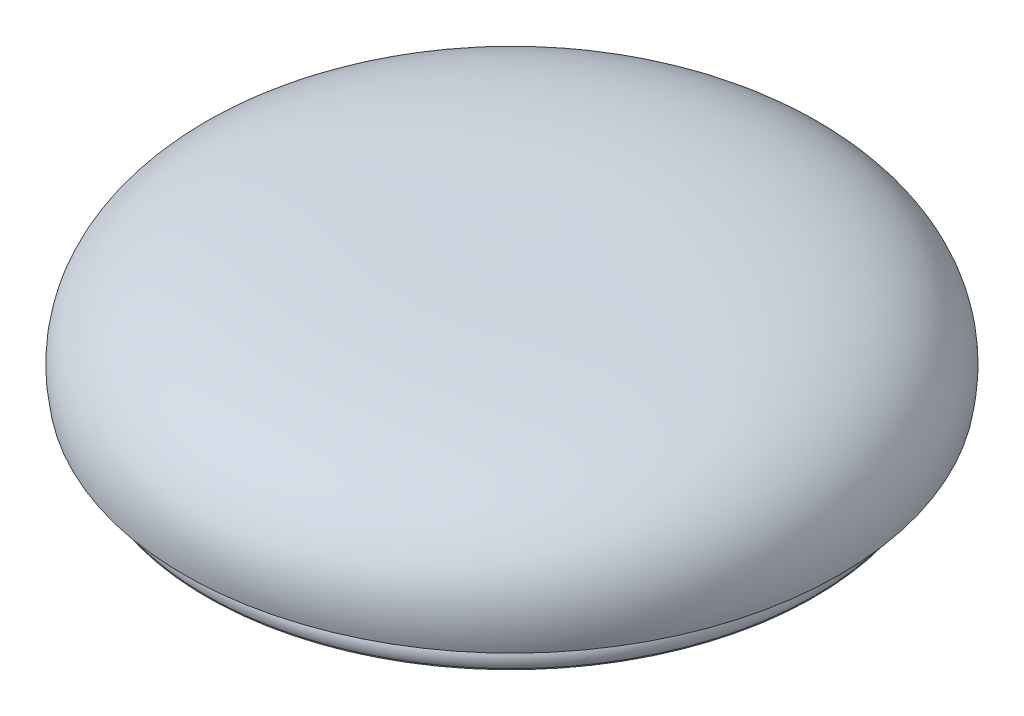
SolidWorks part; units mm, degrees
ref_plane "Front Plane" through (0, 0, 0) normal (0, 0, 1) x (1, 0, 0)
ref_plane "Top Plane" through (0, 0, 0) normal (0, 1, 0) x (1, 0, 0)
ref_plane "Right Plane" through (0, 0, 0) normal (1, 0, 0) x (0, 0, -1)
sketch "Sketch1" plane through (0, 0, 0) normal (0, 0, 1) x (1, 0, 0)
  line L0 (0.0827, -3.4377) -> (0.0827, -9.9585) construction
  line L1 (0.0827, -3.4377) -> (20.5827, -3.4377) construction
  line L2 (0.0827, -3.4377) -> (0.0827, 4.5623) construction
  line L4 (0.0827, 4.5623) -> (5.4646, 4.5623) construction
  line L6 (11.8114, -9.2619) -> (9.3001, -9.2619)
  line L12 (9.3001, -9.2619) -> (9.3001, -9.9585)
  line L13 (9.3001, -9.9585) -> (0.0827, -9.9585)
  line L15 (0.0827, -9.9585) -> (0.0827, 4.5623)
  spline S0 degree 3 poles (16.6015, -7.8371) (17.236, -7.8371) (19.9144, -5.7127) (21.5752, -0.7473) (17.6691, 5.0387) (2.3945, 4.5623) (0.0827, 4.5623) knots 0 0 0 0 0.060344 0.102248 0.311975 0.5003 0.5003 0.5003 0.5003
  spline S1 degree 2 poles (16.6015, -7.8371) (14.2525, -8.7085) (11.8114, -9.2619) knots 0 0 0 1 1 1
  point P4 (0, 0)
  dimension "D1" = 8
  dimension "D2" = 20.5
revolve "Revolve1" add sketch "Sketch1" angle 360 about L15
ref_plane "Plane1" through (0, -3.4377, 0) normal (0, 1, 0) x (1, 0, 0)
split "Split1" trim tools "Plane1" bodies to split 107 resulting bodies 108 109
delete or keep bodies "Body-Delete/Keep 1" type delete bodies bodies 109
shell "Shell1" thickness 1
ref_plane "Plane3" through (0, -1.7377, 0) normal (0, -1, 0) x (-1, 0, 0)
sketch "Sketch11" plane through (0, -3.4377, 0) normal (0, -1, 0) x (-1, 0, 0)
  circle A0 centre (0, 0) radius 19
  dimension "D1" = 38
extrude "Extrude-Thin13" add sketch "Sketch11" along normal blind 2 and the other way up to surface thin other way up to face at (19.5611, -3.4377, 0) thin type one direction reverse wall 1
sketch "Sketch12" plane through (0, -1.7377, 0) normal (0, -1, 0) x (-1, 0, 0)
  circle A0 centre (0, 0) radius 18
extrude "Extrude-Thin14" add sketch "Sketch12" against normal up to surface (3.3343 mm away) thin thin type one direction reverse wall 1
sketch "Sketch13" plane through (0, -1.7377, 0) normal (0, -1, 0) x (-1, 0, 0)
  arc A0 (-17.9722, 0.9996) -> (-17.9722, -0.9996) centre (0, 0) ccw
  circle A9 centre (0, 0) radius 18 construction
  circle A10 centre (0, 0) radius 18 construction
  arc A11 (-0.9996, 17.9722) -> (0.9996, 17.9722) centre (0, 18) ccw
  arc A12 (-17.9722, -0.9996) -> (-17.9722, 0.9996) centre (-18, 0) ccw
  arc A13 (17.9722, 0.9996) -> (17.9722, -0.9996) centre (18, 0) ccw
  arc A14 (0.9996, -17.9722) -> (-0.9996, -17.9722) centre (0, -18) ccw
  arc A15 (-0.9996, -17.9722) -> (0.9996, -17.9722) centre (0, 0) ccw
  arc A16 (0.9996, 17.9722) -> (-0.9996, 17.9722) centre (0, 0) ccw
  arc A17 (17.9722, -0.9996) -> (17.9722, 0.9996) centre (0, 0) ccw
  point P5 (0, 0)
  point P12 (0, 0)
extrude "Boss-Extrude10" add sketch "Sketch13" along normal blind 2
sketch "Sketch14" plane through (0, 0, 0) normal (0, 0, 1) x (1, 0, 0)
  line L0 (-19, -5.4377) -> (19, -5.4377) construction
  line L1 (-18.9688, -5.4377) -> (-18.9688, -4.4339)
  line L2 (0, 0) -> (0, -7.1585) construction
  arc A0 (-18.9688, -5.4377) -> (-18.9688, -4.4339) centre (-18.1039, -4.9358) cw
  dimension "D1" = 1
  dimension "D2" = 1.0038
revolve "Revolve6" add sketch "Sketch14" angle 360 about L2
sketch "Sketch15" plane through (0, -3.4377, 0) normal (0, -1, 0) x (1, 0, 0)
  circle A0 centre (0.0827, 0) radius 19.8781
extrude "Extrude-Thin16" add sketch "Sketch15" against normal blind 3.7 thin thin type one direction reverse wall 1
